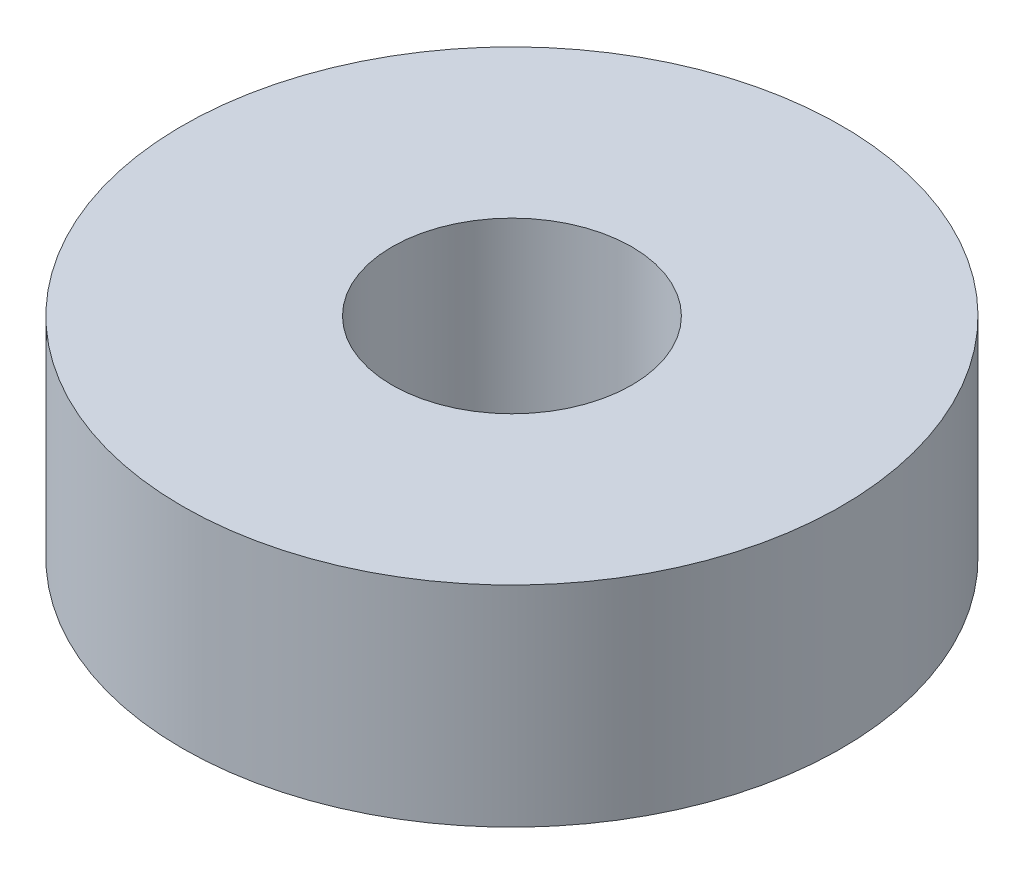
SolidWorks part; units mm, degrees
material "Cast Alloy Steel"
ref_plane "Front Plane" through (0, 0, 0) normal (0, 0, 1) x (1, 0, 0)
ref_plane "Top Plane" through (0, 0, 0) normal (0, 1, 0) x (1, 0, 0)
ref_plane "Right Plane" through (0, 0, 0) normal (1, 0, 0) x (0, 0, -1)
sketch "Sketch1" plane through (0, 0, 0) normal (0, 1, 0) x (1, 0, 0)
  circle A0 centre (0, 0) radius 4
  circle A1 centre (0, 0) radius 11
  dimension "D1" = 8
  dimension "D2" = 22
extrude "Boss-Extrude1" add sketch "Sketch1" along normal mid plane 7
